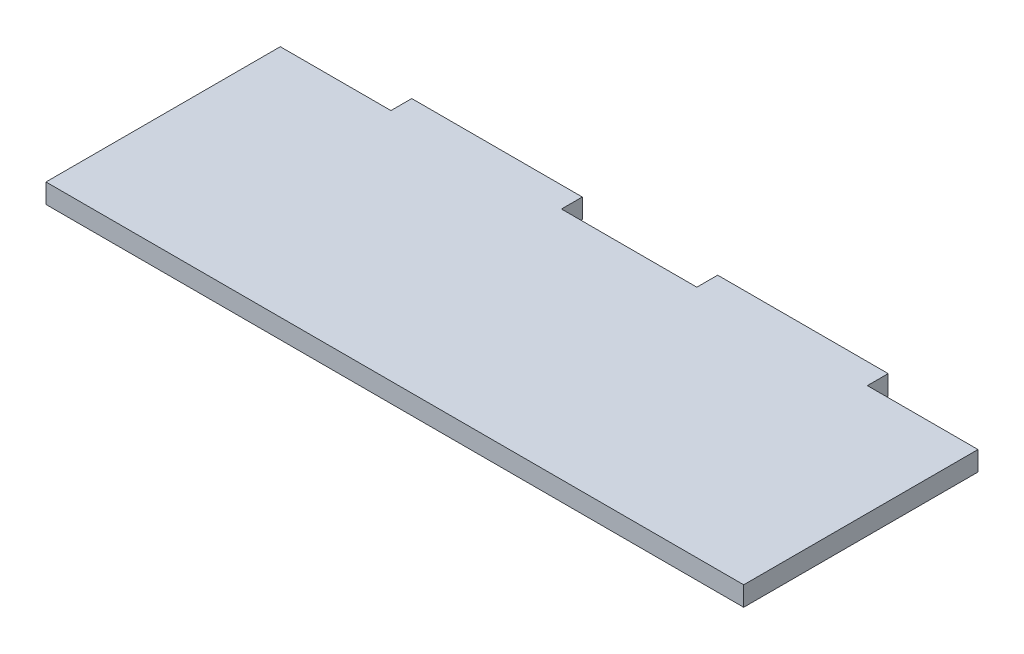
SolidWorks part; units mm, degrees
ref_plane "Front Plane" through (0, 0, 0) normal (0, 0, 1) x (1, 0, 0)
ref_plane "Top Plane" through (0, 0, 0) normal (0, 1, 0) x (1, 0, 0)
ref_plane "Right Plane" through (0, 0, 0) normal (1, 0, 0) x (0, 0, -1)
sketch "Sketch1" plane through (0, 0, 0) normal (0, 1, 0) x (1, 0, 0)
  line L0 (0, 18) -> (8.5, 18)
  line L1 (0, 0) -> (53.6, 0)
  line L5 (8.5, 18) -> (8.5, 19.6)
  line L6 (8.5, 19.6) -> (21.6, 19.6)
  line L7 (21.6, 19.6) -> (21.6, 18)
  line L8 (21.6, 18) -> (32, 18)
  line L9 (32, 18) -> (32, 19.6)
  line L10 (32, 19.6) -> (45.1, 19.6)
  line L11 (45.1, 19.6) -> (45.1, 18)
  line L12 (45.1, 18) -> (53.6, 18)
  line L13 (53.6, 18) -> (53.6, 0)
  line L14 (0, 0) -> (0, 18)
  point P22 (0, 0)
  point P23 (0, 0)
  point P24 (0, 0)
  dimension "D1" = 53.6
  dimension "D2" = 1.6
  dimension "D4" = 8.5
  dimension "D5" = 10.4
  dimension "D6" = 13.1
  dimension "D3" = 18
extrude "Boss-Extrude1" add sketch "Sketch1" along normal blind 1.5
sketch "Slot" plane through (0, 1.5, 0) normal (0, 1, 0) x (1, 0, 0)
  line L15 (23.3, 14.15) -> (30.3, 14.15) construction
  line L16 (23.3, 15.65) -> (30.3, 15.65)
  line L17 (23.3, 12.65) -> (30.3, 12.65)
  line L18 (32, 18) -> (21.6, 18) construction
  arc A0 (23.3, 15.65) -> (23.3, 12.65) centre (23.3, 14.15) ccw
  arc A1 (30.3, 12.65) -> (30.3, 15.65) centre (30.3, 14.15) ccw
  point P5 (26.8, 18)
  point P7 (26.8, 14.15)
  point P20 (21.8, 14.15)
  point P21 (31.8, 14.15)
  point P22 (-12.1751, -8.8981)
  point P23 (-12.1751, -8.8981)
  point P24 (-12.1751, -8.8981)
  dimension "D8" = 10
  dimension "D1" = 5.35
  dimension "D7" = 3
equation "\"margin\"= 0.2"
equation "\"height\"= 18"
equation "\"length\"= 113"
equation "\"tabwidth\"= 10"
equation "\"D4@Sketch1\"= \"tabwidth\" + \"margin\" - \"thick\" - \"margin\""
equation "\"D5@Sketch1\"=\"tabwidth\"+(2*\"margin\")"
equation "\"D3@Sketch1\"=\"height\""
equation "\"width\"= 57"
equation "\"D1@Sketch1\" = \"width\" - 2 * ( \"thick\" + \"margin\" )"
equation "\"thick\"= 1.5"
equation "\"D2@Sketch1\"=\"thick\"+(\"margin\"/2)"
equation "\"D1@Boss-Extrude1\"=\"thick\""
